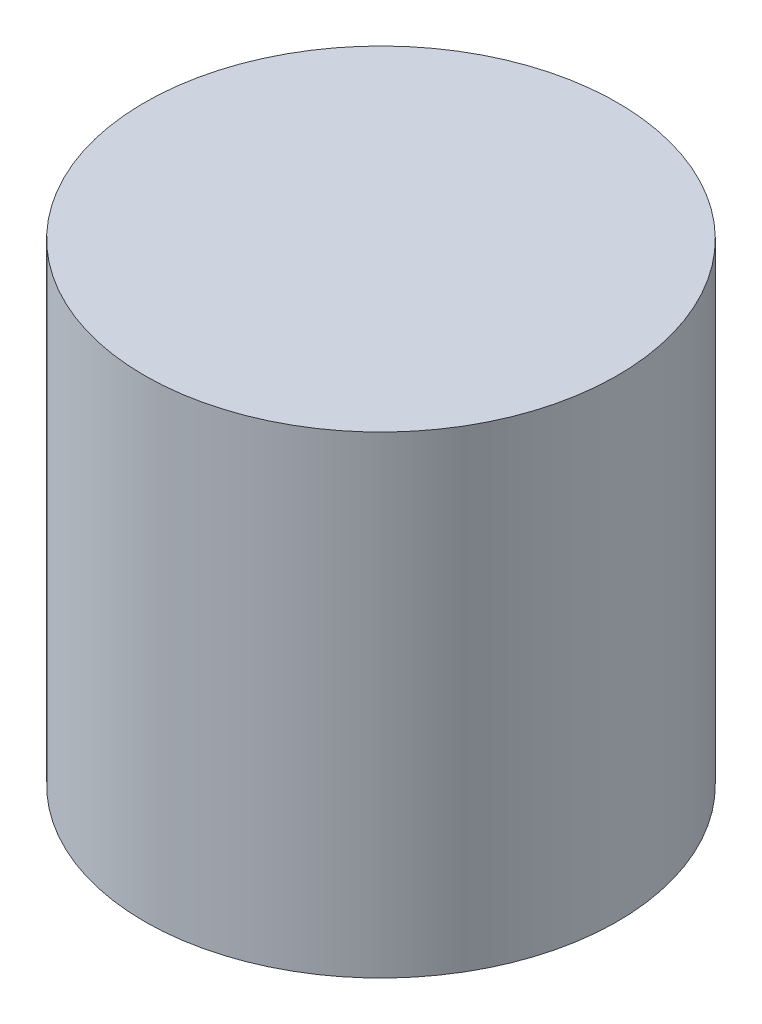
SolidWorks part; units mm, degrees
ref_plane "Front Plane" through (0, 0, 0) normal (0, 0, 1) x (1, 0, 0)
ref_plane "Top Plane" through (0, 0, 0) normal (0, 1, 0) x (1, 0, 0)
ref_plane "Right Plane" through (0, 0, 0) normal (1, 0, 0) x (0, 0, -1)
sketch "Sketch1" plane through (0, 0, 0) normal (0, 1, 0) x (1, 0, 0)
  circle A0 centre (0, 0) radius 25
  dimension "D1" = 50
extrude "Boss-Extrude1" add sketch "Sketch1" along normal blind 50
